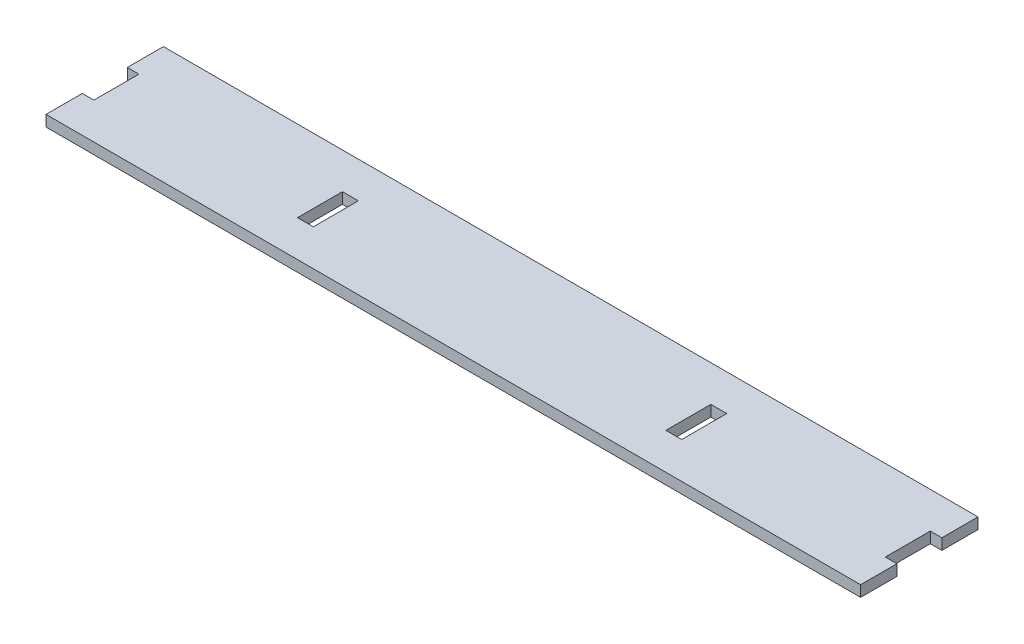
SolidWorks part; units mm, degrees
material "Plain Carbon Steel"
ref_plane "Front Plane" through (0, 0, 0) normal (0, 0, 1) x (1, 0, 0)
ref_plane "Top Plane" through (0, 0, 0) normal (0, 1, 0) x (1, 0, 0)
ref_plane "Right Plane" through (0, 0, 0) normal (1, 0, 0) x (0, 0, -1)
sketch "Sketch1" plane through (0, 0, 0) normal (0, 1, 0) x (1, 0, 0)
  line L0 (0, 25.4) -> (0, 0) construction
  line L1 (-177.8, 25.4) -> (177.8, 25.4)
  line L2 (-177.8, 25.4) -> (-177.8, -25.4)
  line L3 (-177.8, -25.4) -> (177.8, -25.4)
  line L4 (177.8, 25.4) -> (177.8, -25.4)
  line L5 (0, 0) -> (177.8, 0) construction
  dimension "D1" = 177.8
  dimension "D2" = 25.4
extrude "Boss-Extrude1" add sketch "Sketch1" along normal blind 4.7625
sketch "Sketch2" plane through (0, 0, 0) normal (0, -1, 0) x (-1, 0, 0)
  line L0 (-177.8, -25.4) -> (-177.8, 25.4) construction
  line L1 (-171.45, 9.525) -> (-177.8, 9.525)
  line L2 (-171.45, 9.525) -> (-171.45, -9.4383)
  line L3 (-171.45, -9.4383) -> (-177.8, -9.4383)
  line L4 (-177.8, 9.525) -> (-177.8, -9.4383)
  line L5 (-177.8, -9.4383) -> (-171.45, -9.4383) construction
  line L6 (171.45, -9.4383) -> (177.8, -9.4383) construction
  line L7 (-82.55, 9.525) -> (-76.2, 9.525)
  line L8 (-82.55, 9.525) -> (-82.55, -9.4383)
  line L9 (-82.55, -9.4383) -> (-76.2, -9.4383)
  line L10 (-76.2, 9.525) -> (-76.2, -9.4383)
  line L11 (76.2, 9.525) -> (82.55, 9.525)
  line L12 (76.2, 9.525) -> (76.2, -9.4383)
  line L13 (76.2, -9.4383) -> (82.55, -9.4383)
  line L14 (82.55, 9.525) -> (82.55, -9.4383)
  line L15 (171.45, 9.525) -> (177.8, 9.525)
  line L16 (171.45, 9.525) -> (171.45, -9.4383)
  line L17 (171.45, -9.4383) -> (177.8, -9.4383)
  line L18 (177.8, 9.525) -> (177.8, -9.4383)
  line L19 (177.8, 25.4) -> (177.8, -25.4) construction
  line L20 (171.196, 9.779) -> (171.196, -9.6923)
  line L21 (171.196, -9.6923) -> (178.054, -9.6923)
  line L22 (178.054, 9.779) -> (178.054, -9.6923)
  line L23 (171.196, 9.779) -> (178.054, 9.779)
  line L24 (75.946, 9.779) -> (75.946, -9.6923)
  line L25 (75.946, -9.6923) -> (82.804, -9.6923)
  line L26 (82.804, 9.779) -> (82.804, -9.6923)
  line L27 (75.946, 9.779) -> (82.804, 9.779)
  line L28 (-82.804, 9.779) -> (-82.804, -9.6923)
  line L29 (-82.804, -9.6923) -> (-75.946, -9.6923)
  line L30 (-75.946, 9.779) -> (-75.946, -9.6923)
  line L31 (-82.804, 9.779) -> (-75.946, 9.779)
  line L32 (-171.196, 9.779) -> (-171.196, -9.6923)
  line L33 (-171.196, -9.6923) -> (-178.054, -9.6923)
  line L34 (-178.054, 9.779) -> (-178.054, -9.6923)
  line L35 (-171.196, 9.779) -> (-178.054, 9.779)
  dimension "D1" = 0.254
extrude "Cut-Extrude1" cut sketch "Sketch2" against normal through all
sketch "Sketch3" plane through (0, 4.7625, 0) normal (0, 1, 0) x (1, 0, 0)
  line L0 (-176.2125, -25.4) -> (-176.2125, 25.4)
  line L1 (176.2125, 25.4) -> (176.2125, -25.4)
  line L12 (171.196, 9.779) -> (177.8, 9.779)
  line L13 (177.8, 9.779) -> (177.8, 25.4)
  line L14 (177.8, 25.4) -> (-177.8, 25.4)
  line L15 (-177.8, 25.4) -> (-177.8, 9.779)
  line L16 (-177.8, 9.779) -> (-171.196, 9.779)
  line L17 (-171.196, 9.779) -> (-171.196, -9.6923)
  line L18 (-171.196, -9.6923) -> (-177.8, -9.6923)
  line L19 (-177.8, -9.6923) -> (-177.8, -25.4)
  line L20 (-177.8, -25.4) -> (177.8, -25.4)
  line L21 (177.8, -25.4) -> (177.8, -9.6923)
  line L22 (177.8, -9.6923) -> (171.196, -9.6923)
  line L23 (171.196, -9.6923) -> (171.196, 9.779)
  line L24 (171.196, 9.779) -> (177.8, 9.779)
  line L25 (177.8, 9.779) -> (177.8, 25.4)
  line L26 (177.8, 25.4) -> (-177.8, 25.4)
  line L27 (-177.8, 25.4) -> (-177.8, 9.779)
  line L28 (-177.8, 9.779) -> (-171.196, 9.779)
  line L29 (-171.196, 9.779) -> (-171.196, -9.6923)
  line L30 (-171.196, -9.6923) -> (-177.8, -9.6923)
  line L31 (-177.8, -9.6923) -> (-177.8, -25.4)
  line L32 (-177.8, -25.4) -> (177.8, -25.4)
  line L33 (177.8, -25.4) -> (177.8, -9.6923)
  line L34 (177.8, -9.6923) -> (171.196, -9.6923)
  line L35 (171.196, -9.6923) -> (171.196, 9.779)
  line M13 (171.196, 9.779) -> (177.8, 9.779)
  line M14 (177.8, 9.779) -> (177.8, 25.4)
  line M15 (177.8, 25.4) -> (-177.8, 25.4)
  line M16 (-177.8, 25.4) -> (-177.8, 9.779)
  line M17 (-177.8, 9.779) -> (-171.196, 9.779)
  line M19 (-171.196, -9.6923) -> (-177.8, -9.6923)
  line M20 (-177.8, -9.6923) -> (-177.8, -25.4)
  line M21 (-177.8, -25.4) -> (177.8, -25.4)
  line M22 (177.8, -25.4) -> (177.8, -9.6923)
  line M23 (177.8, -9.6923) -> (171.196, -9.6923)
  dimension "D2" = 1.5875
  dimension "D3" = 1.5875
  dimension "D1" = 0
extrude "Cut-Extrude2" cut sketch "Sketch3" against normal through all contours L0 M21 M19 M20 | L0 M17 M15 M16 | L1 M23 M21 M22 | L1 M15 M13 M14
sketch "Sketch4" plane through (0, 4.7625, 0) normal (0, 1, 0) x (1, 0, 0)
  line L0 (-75.946, -9.6923) -> (-82.804, -9.6923) construction
  line L1 (-75.946, 9.779) -> (-76.2635, 9.779)
  line L2 (-75.946, 9.779) -> (-75.946, -9.6923)
  line L3 (-75.946, -9.6923) -> (-76.2635, -9.6923)
  line L4 (-76.2635, 9.779) -> (-76.2635, -9.6923)
  line L5 (82.804, -9.6923) -> (75.946, -9.6923) construction
  line L6 (75.946, 9.779) -> (76.2635, 9.779)
  line L7 (75.946, 9.779) -> (75.946, -9.6923)
  line L8 (75.946, -9.6923) -> (76.2635, -9.6923)
  line L9 (76.2635, 9.779) -> (76.2635, -9.6923)
  dimension "D1" = 152.527
extrude "Boss-Extrude2" add sketch "Sketch4" against normal up to surface (4.7625 mm away) up to face at (79.375, 0, -0.0433)
sketch "Sketch5" plane through (0, 4.7625, 0) normal (0, 1, 0) x (1, 0, 0)
  line L0 (82.804, -9.6923) -> (76.2635, -9.6923) construction
  line L1 (-82.804, 9.779) -> (-83.1215, 9.779)
  line L2 (-82.804, 9.779) -> (-82.804, -9.6923)
  line L3 (-82.804, -9.6923) -> (-83.1215, -9.6923)
  line L4 (-83.1215, 9.779) -> (-83.1215, -9.6923)
  line L5 (82.804, 9.779) -> (83.1215, 9.779)
  line L6 (82.804, 9.779) -> (82.804, -9.6923)
  line L7 (82.804, -9.6923) -> (83.1215, -9.6923)
  line L8 (83.1215, 9.779) -> (83.1215, -9.6923)
  line L9 (-76.2635, 9.779) -> (-76.2635, -9.6923) construction
  dimension "D1" = 6.858
extrude "Cut-Extrude4" cut sketch "Sketch5" against normal through all
